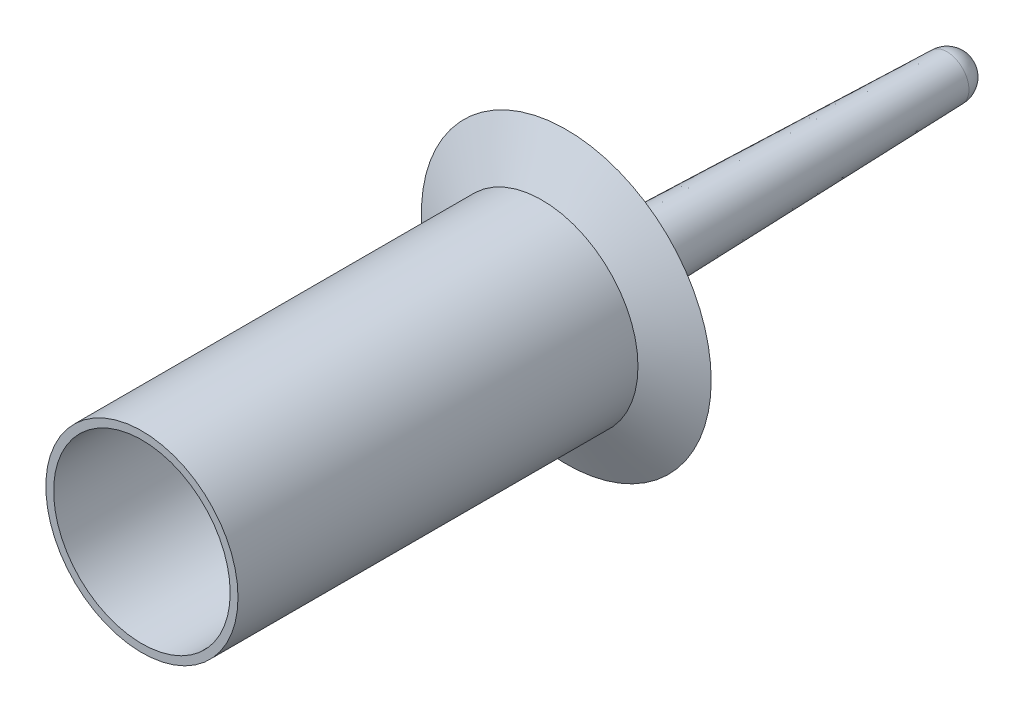
SolidWorks part; units mm, degrees
ref_plane "Front Plane" through (0, 0, 0) normal (0, 0, 1) x (1, 0, 0)
ref_plane "Top Plane" through (0, 0, 0) normal (0, 1, 0) x (1, 0, 0)
ref_plane "Right Plane" through (0, 0, 0) normal (1, 0, 0) x (0, 0, -1)
sketch "Sketch1" plane through (0, 0, 0) normal (0, 1, 0) x (1, 0, 0)
  line L0 (0, -52.0446) -> (0, 52.0446) construction
  line L1 (25.0063, 52.0446) -> (37.7063, 58.3946)
  line L2 (22.9743, 52.0446) -> (25.0063, 52.0446)
  line L3 (22.9743, 52.0446) -> (22.9743, -52.0446)
  line L4 (22.9743, -52.0446) -> (25.0063, -52.0446)
  line L5 (25.0063, 52.0446) -> (25.0063, -52.0446)
  line L6 (37.7063, 58.3946) -> (14.8613, 58.3305)
  line L7 (8.4963, 64.4906) -> (5.715, 157.4546)
  line L8 (0, 52.0446) -> (0, 157.4546) construction
  line L9 (22.9743, 52.0446) -> (0, 52.0446)
  line L10 (0, 52.0446) -> (0, 163.1696)
  arc A0 (14.8613, 58.3305) -> (8.4963, 64.4906) centre (14.8435, 64.6805) cw
  arc A1 (5.715, 157.4546) -> (0, 163.1696) centre (0, 157.4546) ccw
  point P4 (0, 0)
  dimension "D6" = 6.35
  dimension "D1" = 104.0892
  dimension "D2" = 45.9486
  dimension "D3" = 2.032
  dimension "D4" = 12.7
  dimension "D5" = 6.35
  dimension "D7" = 29.21
  dimension "D8" = 99.06
  dimension "D9" = 11.43
  dimension "D10" = 6.096
revolve "Revolve1" add sketch "Sketch1" angle 360 about L0
